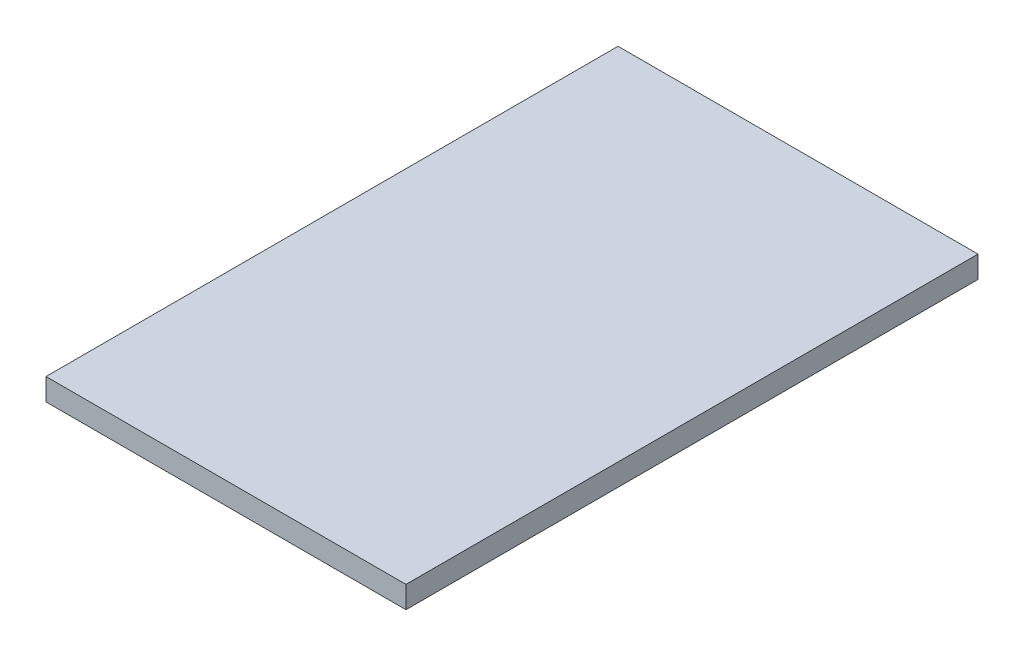
SolidWorks part; units mm, degrees
ref_plane "Front Plane" through (0, 0, 0) normal (0, 0, 1) x (1, 0, 0)
ref_plane "Top Plane" through (0, 0, 0) normal (0, 1, 0) x (1, 0, 0)
ref_plane "Right Plane" through (0, 0, 0) normal (1, 0, 0) x (0, 0, -1)
sketch "Sketch1" plane through (0, 0, 0) normal (0, 1, 0) x (1, 0, 0)
  line L1 (0, 0) -> (26.2128, 0)
  line L2 (0, 0) -> (0, 41.656)
  line L3 (0, 41.656) -> (26.2128, 41.656)
  line L4 (26.2128, 0) -> (26.2128, 41.656)
  dimension "D1" = 41.656
  dimension "D2" = 26.2128
extrude "Boss-Extrude1" add sketch "Sketch1" along normal blind 1.6002
